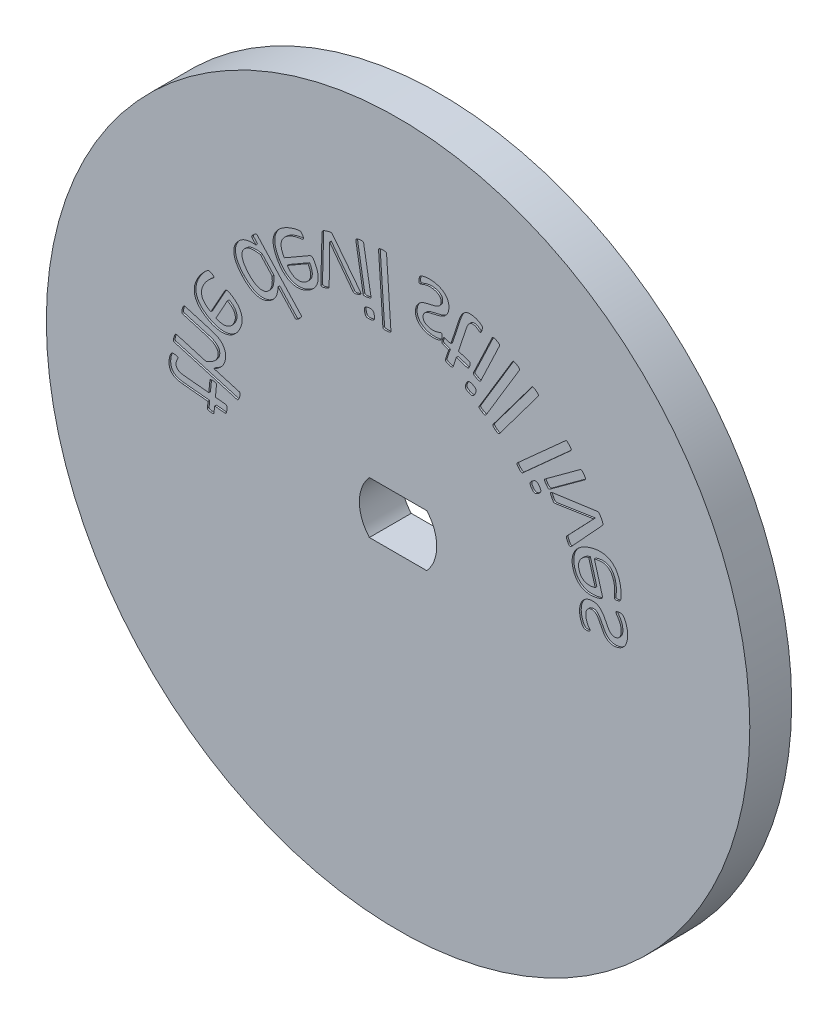
SolidWorks part; units mm, degrees
ref_plane "Front Plane" through (0, 0, 0) normal (0, 0, 1) x (1, 0, 0)
ref_plane "Top Plane" through (0, 0, 0) normal (0, 1, 0) x (1, 0, 0)
ref_plane "Right Plane" through (0, 0, 0) normal (1, 0, 0) x (0, 0, -1)
sketch "Sketch1" plane through (0, 0, 0) normal (0, 0, 1) x (1, 0, 0)
  line L1 (-2.1752, 1.9685) -> (2.1752, 1.9685)
  line L2 (-2.1752, 1.9685) -> (-2.1752, -1.9685)
  line L3 (-2.1752, -1.9685) -> (2.1752, -1.9685)
  line L4 (2.1752, 1.9685) -> (2.1752, -1.9685)
  circle A0 centre (0, 0) radius 26.67
  arc A1 (2.1752, -1.9685) -> (2.1752, 1.9685) centre (0, 0) ccw
  arc A2 (-2.1752, 1.9685) -> (-2.1752, -1.9685) centre (0, 0) ccw
  dimension "D1" = 53.34
  dimension "D2" = 2.9337
  dimension "D3" = 3.937
extrude "Boss-Extrude1" add sketch "Sketch1" along normal blind 3.175 contours A0 A2 L1 A1 L3
sketch "Sketch2" plane through (0, 0, 3.175) normal (0, 0, 1) x (1, 0, 0)
  circle A0 centre (0, 0) radius 17.4625 construction
  text T0 "the devil still lives" font "Calibri" height in points 18
  dimension "D1" = 34.925
extrude "Cut-Extrude1" cut sketch "Sketch2" against normal blind 0.127
